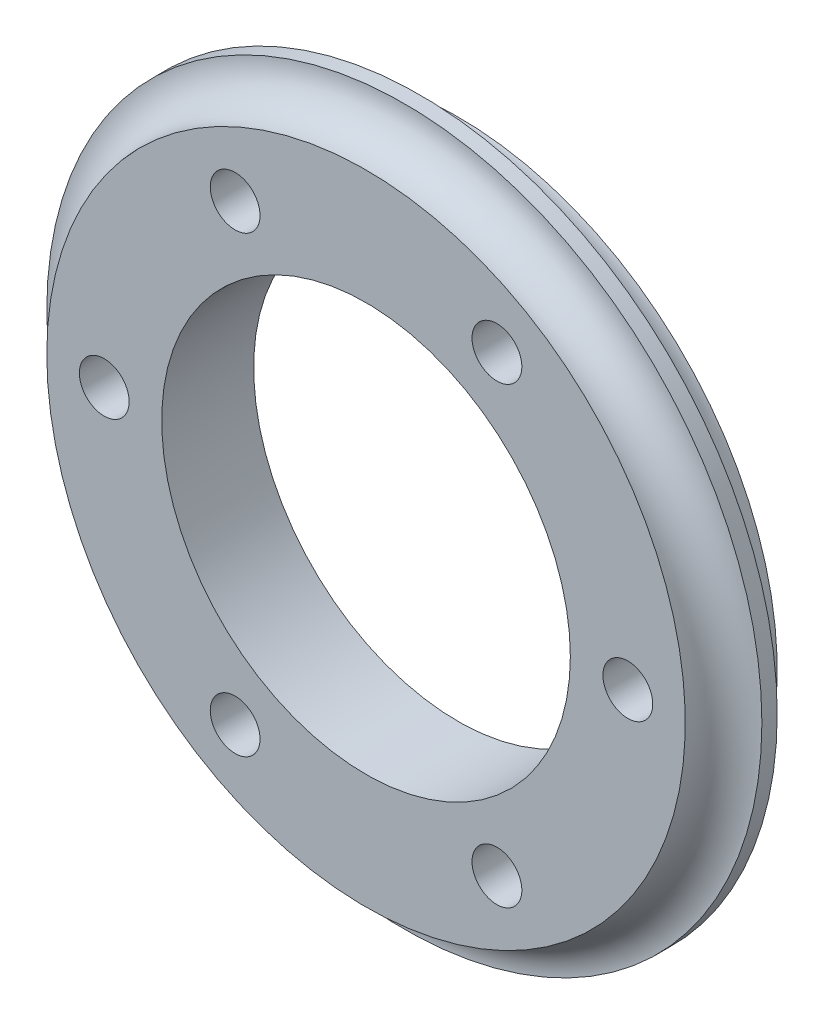
SolidWorks part; units mm, degrees
ref_plane "Front Plane" through (0, 0, 0) normal (0, 0, 1) x (1, 0, 0)
ref_plane "Top Plane" through (0, 0, 0) normal (0, 1, 0) x (1, 0, 0)
ref_plane "Right Plane" through (0, 0, 0) normal (1, 0, 0) x (0, 0, -1)
sketch "Sketch2" plane through (0, 0, 0) normal (0, 0, 1) x (1, 0, 0)
  circle A0 centre (0, 0) radius 13.335
  circle A1 centre (0, 0) radius 23.335
  dimension "D1" = 26.67
  dimension "D2" = 10
extrude "Boss-Extrude1" add sketch "Sketch2" along normal blind 6
ref_axis "Axis1" through (0, 0, 6) along (0, 0, -1)
sketch "Sketch3" plane through (0, 0, 0) normal (0, 1, 0) x (1, 0, 0)
  circle A0 centre (-23.335, 0) radius 2.5
  circle A1 centre (-23.335, -6) radius 2.5
  dimension "D1" = 5
revolve "Cut-Revolve1" cut sketch "Sketch3" angle 360 about axis through (0, 0, 6) along (0, 0, -1)
sketch "Sketch4" plane through (0, 0, 0) normal (0, 0, -1) x (-1, 0, 0)
  line L0 (13.335, 0) -> (20.835, 0) construction
  line L1 (17.085, 0) -> (8.5425, 14.796) construction
  line L2 (8.5425, 14.796) -> (-8.5425, 14.796) construction
  line L3 (-8.5425, 14.796) -> (-17.085, 0) construction
  line L4 (-17.085, 0) -> (-8.5425, -14.796) construction
  line L5 (-8.5425, -14.796) -> (8.5425, -14.796) construction
  line L6 (8.5425, -14.796) -> (17.085, 0) construction
  circle A0 centre (0, 0) radius 14.796 construction
  circle A1 centre (0, 0) radius 13.335 construction
  circle A2 centre (0, 0) radius 20.835 construction
  circle A3 centre (8.5425, 14.796) radius 1.625
  circle A4 centre (-8.5425, 14.796) radius 1.625
  circle A5 centre (-17.085, 0) radius 1.625
  circle A6 centre (-8.5425, -14.796) radius 1.625
  circle A7 centre (8.5425, -14.796) radius 1.625
  circle A8 centre (17.085, 0) radius 1.625
  dimension "D1" = 3.25
extrude "Cut-Extrude1" cut sketch "Sketch4" against normal through all
